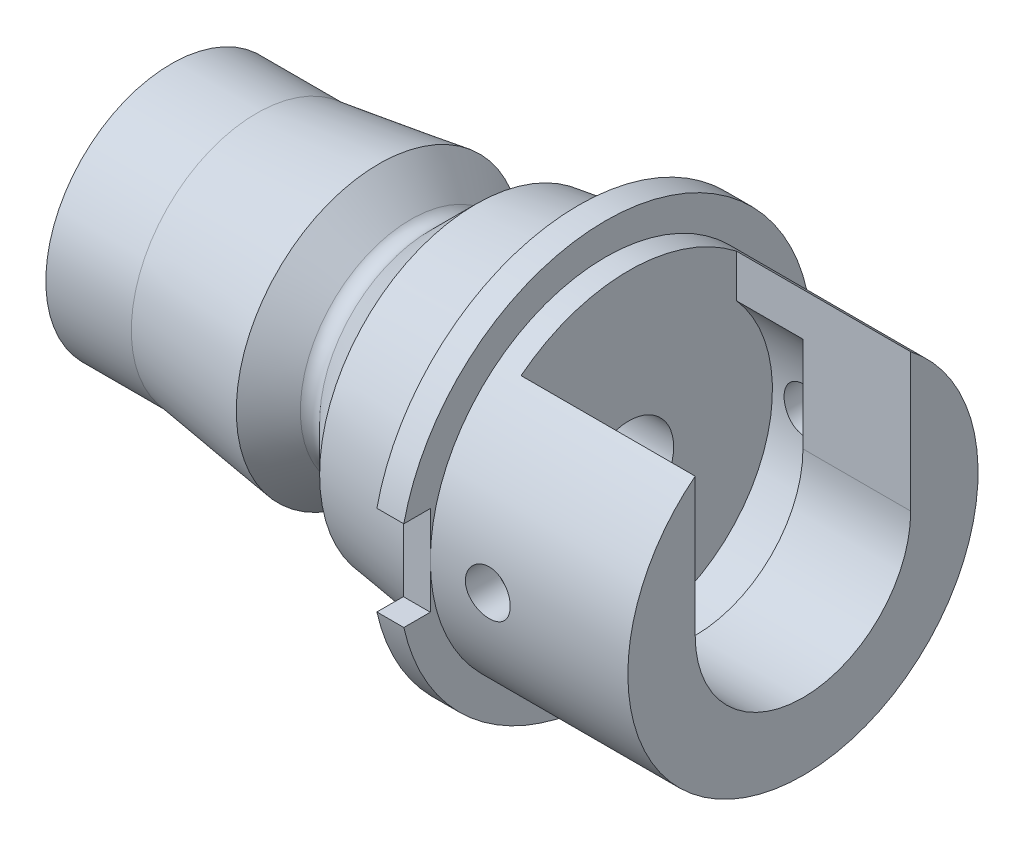
SolidWorks part; units mm, degrees
ref_plane "Front Plane" through (0, 0, 0) normal (0, 0, 1) x (1, 0, 0)
ref_plane "Top Plane" through (0, 0, 0) normal (0, 1, 0) x (1, 0, 0)
ref_plane "Right Plane" through (0, 0, 0) normal (1, 0, 0) x (0, 0, -1)
sketch "Sketch1" plane through (0, 0, 0) normal (0, 0, 1) x (1, 0, 0)
  line L0 (0, 0) -> (0, 6.982)
  line L1 (0, 6.982) -> (4.76, 6.982)
  line L2 (4.76, 6.982) -> (11.56, 7.9377)
  line L3 (11.56, 7.9377) -> (13.3431, 6.1545)
  line L4 (11.56, 7.9377) -> (23.1675, 9.569) construction
  line L5 (16.96, 8.6966) -> (22.6765, 9.5)
  line L6 (4.76, 6.982) -> (7.8351, 6.982) construction
  line L7 (11.56, 7.9377) -> (15.4875, 7.9377) construction
  line L8 (16.96, 8.6966) -> (14.4179, 6.1545)
  line L9 (16.96, 8.6966) -> (14.3792, 8.6966) construction
  line L10 (14.4179, 6.1545) -> (13.8805, 6.6919) construction
  line L11 (13.8805, 6.6919) -> (13.3431, 6.1545) construction
  line L12 (22.6765, 9.5) -> (22.6765, 11.5)
  line L13 (22.6765, 11.5) -> (24.1765, 11.5)
  line L14 (24.1765, 11.5) -> (24.1765, 0)
  line L15 (0, 0) -> (31.0457, 0) construction
  line L16 (24.1765, 0) -> (0, 0)
  line L17 (0, 0) -> (71.6905, 0) construction
  arc A0 (14.4179, 6.1545) -> (13.3431, 6.1545) centre (13.8805, 6.6919) cw
  dimension "D1" = 6.982
  dimension "D2" = 4.76
  dimension "D3" = 11.56
  dimension "D4" = 16.96
  dimension "D5" = 8
  dimension "D6" = 45
  dimension "D7" = 45
  dimension "D8" = 0.76
  dimension "D9" = 9.5
  dimension "D10" = 11.5
  dimension "D11" = 1.5
revolve "Revolve3" add sketch "Sketch1" angle 360 about L16
sketch "Sketch3" plane through (24.1765, 0, 0) normal (1, 0, 0) x (0, 0, -1)
  line L0 (0, 0) -> (15.7286, 0) construction
  line L1 (0, 0) -> (-16.4314, 0) construction
  line L2 (-11.75, 2.5) -> (-9.75, 2.5)
  line L3 (9.75, 2.5) -> (11.75, 2.5)
  line L4 (9.75, 2.5) -> (9.75, -2.5)
  line L5 (9.75, -2.5) -> (11.75, -2.5)
  line L6 (11.75, 2.5) -> (11.75, -2.5)
  line L7 (-11.75, 2.5) -> (-11.75, -2.5)
  line L8 (-11.75, -2.5) -> (-9.75, -2.5)
  line L9 (-9.75, 2.5) -> (-9.75, -2.5)
  point P8 (11.75, 0)
  point P13 (-9.75, 0)
  dimension "D1" = 2
  dimension "D2" = 5
  dimension "D3" = 9.75
  dimension "D4" = 2
  dimension "D5" = 9.75
extrude "Slots" cut sketch "Sketch3" against normal through all
sketch "Sketch4" plane through (24.1765, 0, 0) normal (1, 0, 0) x (0, 0, -1)
  circle A0 centre (0, 0) radius 9.75
  dimension "D1" = 19.5
extrude "Holder" add sketch "Sketch4" along normal blind 11
sketch "Sketch5" plane through (35.1765, 0, 0) normal (1, 0, 0) x (0, 0, -1)
  line L0 (6, 0) -> (6, 7.6852)
  line L1 (-6, 0) -> (-6, 7.6852)
  arc A0 (-6, 0) -> (6, 0) centre (0, 0) ccw
  arc A1 (6, 7.6852) -> (-6, 7.6852) centre (0, 0) ccw
  dimension "D1" = 12
  dimension "D2" = 19.5
extrude "Holder Slot" cut sketch "Sketch5" against normal blind 9.7
sketch "Sketch6" plane through (25.4765, 0, 0) normal (1, 0, 0) x (0, 0, -1)
  circle A0 centre (0, 0) radius 8
  dimension "D1" = 16
extrude "Cut-Extrude8" cut sketch "Sketch6" along normal blind 3.7
sketch "Sketch2" plane through (0, 0, 0) normal (1, 0, 0) x (0, 0, -1)
  circle A0 centre (0, 0) radius 2.5
  dimension "D1" = 5
extrude "Cut-Extrude9" cut sketch "Sketch2" along normal through all
ref_plane "Plane1" through (0, 0, 10) normal (0, 0, 1) x (1, 0, 0)
hole_wizard "M3x0.5 Tapped Hole1" positions "Sketch7" profile "Sketch8" tap size "M3x0.5" standard "ANSI Metric"
sketch "Sketch7" plane through (0, 0, 10) normal (0, 0, 1) x (1, 0, 0)
  line L0 (0, 0) -> (36.489, 0) construction
  line L1 (35.1765, -9.75) -> (35.1765, 7.6852) construction
  point P6 (27.3765, 0)
  dimension "D1" = 7.8
sketch "Sketch8" plane through (27.3765, 0, 10) normal (1, 0, 0) x (0, -1, 0)
  line L0 (0, 0) -> (0, 2)
  line L1 (0, 2) -> (1.25, 2)
  line L2 (1.25, 2) -> (1.25, 0)
  line L5 (1.25, 0) -> (0, 0)
  line L11 (0, -6.35) -> (0, 107.95) construction
  dimension "Thru Tap Drill Dia." = 2.5
  dimension "Thru Tap Drill Depth" = 2
cosmetic thread "Hole Thread1" parameters "D2"=3
ref_plane "Plane2" through (0, 0, -10) normal (0, 0, 1) x (1, 0, 0)
hole_wizard "M3x0.5 Tapped Hole2" positions "Sketch9" profile "Sketch10" tap size "M3x0.5" standard "ANSI Metric"
sketch "Sketch9" plane through (0, 0, -10) normal (0, 0, 1) x (1, 0, 0)
  line L0 (0, 0) -> (36.1163, 0) construction
  line L1 (35.1765, -9.75) -> (35.1765, 7.6852) construction
  point P5 (27.3765, 0)
  dimension "D1" = 7.8
sketch "Sketch10" plane through (27.3765, 0, -10) normal (1, 0, 0) x (0, 1, 0)
  line L0 (0, 0) -> (0, 2)
  line L1 (0, 2) -> (1.25, 2)
  line L2 (1.25, 2) -> (1.25, 0)
  line L5 (1.25, 0) -> (0, 0)
  line L11 (0, -6.35) -> (0, 107.95) construction
  dimension "Thru Tap Drill Dia." = 2.5
  dimension "Thru Tap Drill Depth" = 2
cosmetic thread "Hole Thread2" parameters "D2"=3
ref_plane "Plane3" through (0, -10, 0) normal (0, 1, 0) x (1, 0, 0)
hole_wizard "M3x0.5 Tapped Hole3" positions "Sketch11" profile "Sketch12" tap size "M3x0.5" standard "ANSI Metric"
sketch "Sketch11" plane through (0, -10, 0) normal (0, 1, 0) x (1, 0, 0)
  line L0 (0, 0) -> (35.8086, 0) construction
  line L1 (35.1765, -9.75) -> (35.1765, 9.75) construction
  point P6 (27.3765, 0)
  dimension "D1" = 7.8
sketch "Sketch12" plane through (27.3765, -10, 0) normal (1, 0, 0) x (0, 0, -1)
  line L0 (0, 0) -> (0, 2)
  line L1 (0, 2) -> (1.25, 2)
  line L2 (1.25, 2) -> (1.25, 0)
  line L5 (1.25, 0) -> (0, 0)
  line L11 (0, -6.35) -> (0, 107.95) construction
  dimension "Thru Tap Drill Dia." = 2.5
  dimension "Thru Tap Drill Depth" = 2
cosmetic thread "Hole Thread3" parameters "D2"=3
